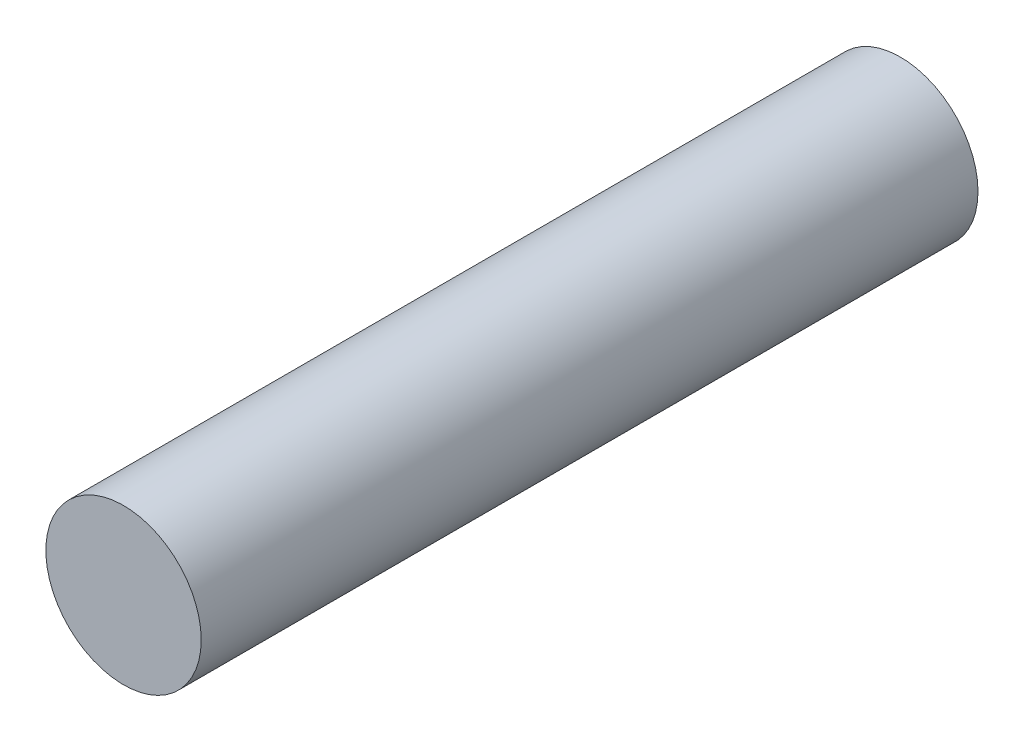
SolidWorks part; units mm, degrees
ref_plane "前视基准面" through (0, 0, 0) normal (0, 0, 1) x (1, 0, 0)
ref_plane "上视基准面" through (0, 0, 0) normal (0, 1, 0) x (1, 0, 0)
ref_plane "右视基准面" through (0, 0, 0) normal (1, 0, 0) x (0, 0, -1)
sketch "草图1" plane through (0, 0, 0) normal (0, 0, 1) x (1, 0, 0)
  circle A0 centre (0, 0) radius 1
extrude "凸台-拉伸1" add sketch "草图1" along normal blind 10
